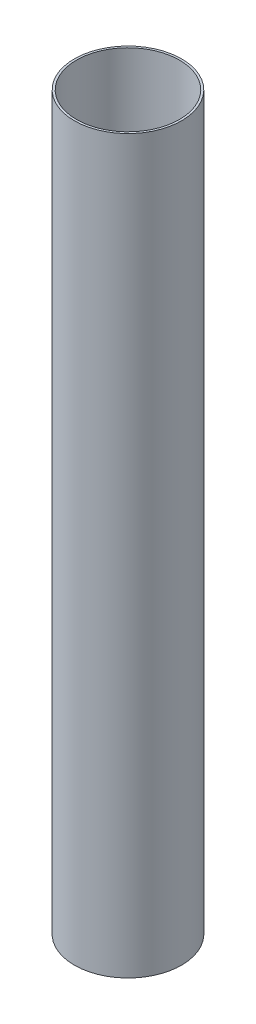
SolidWorks part; units mm, degrees
ref_plane "Front Plane" through (0, 0, 0) normal (0, 0, 1) x (1, 0, 0)
ref_plane "Top Plane" through (0, 0, 0) normal (0, 1, 0) x (1, 0, 0)
ref_plane "Right Plane" through (0, 0, 0) normal (1, 0, 0) x (0, 0, -1)
sketch "Sketch1" plane through (0, 0, 0) normal (0, 1, 0) x (1, 0, 0)
  circle A0 centre (0, 0) radius 39.6748
  circle A1 centre (0, 0) radius 38.1
  dimension "D1" = 76.2
  dimension "D2" = 79.3496
extrude "Boss-Extrude1" add sketch "Sketch1" along normal mid plane 541.02
equation "\"oDiameter\" = 3.124in"
equation "\"iDiameter\"= 3in"
equation "\"length\"= 21.3in"
equation "\"D1@Sketch1\"=\"iDiameter\""
equation "\"D2@Sketch1\"=\"oDiameter\""
